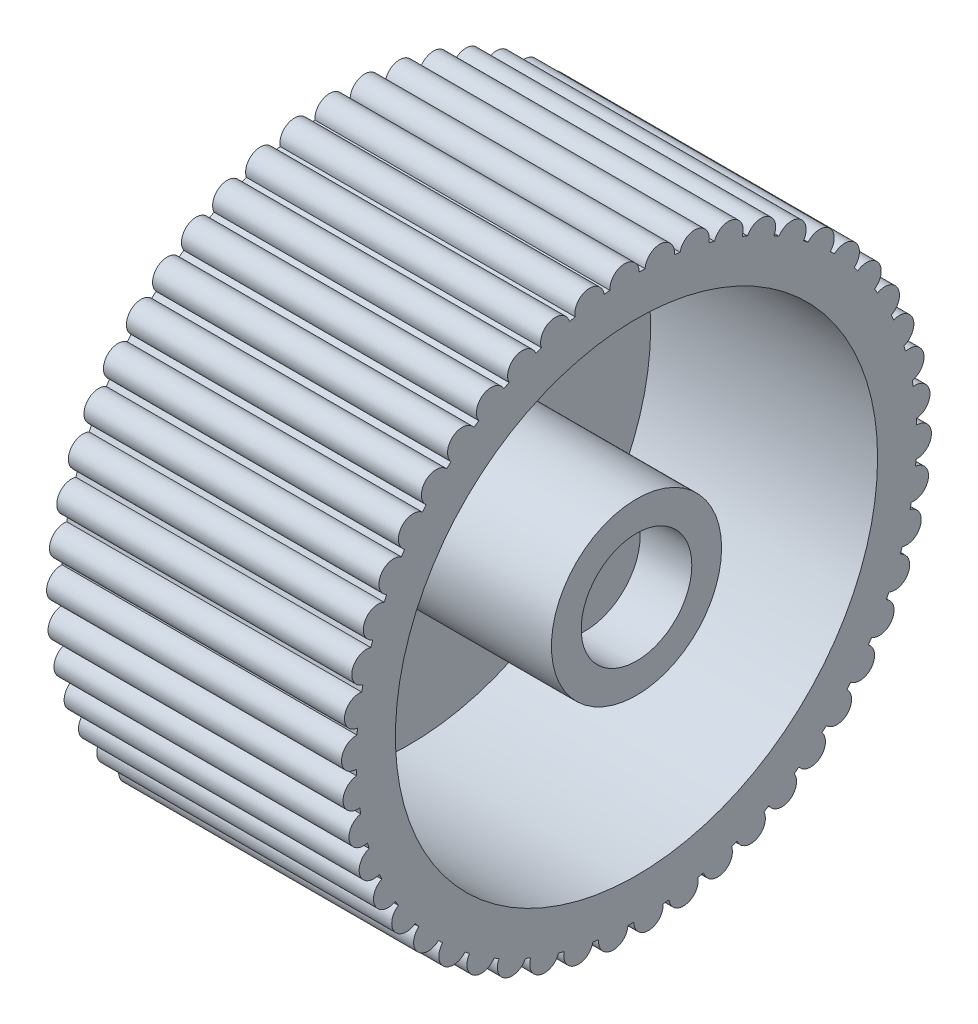
SolidWorks part; units mm, degrees
ref_plane "Front Plane" through (0, 0, 0) normal (0, 0, 1) x (1, 0, 0)
ref_plane "Top Plane" through (0, 0, 0) normal (0, 1, 0) x (1, 0, 0)
ref_plane "Right Plane" through (0, 0, 0) normal (1, 0, 0) x (0, 0, -1)
sketch "Sketch1" plane through (0, 0, 0) normal (1, 0, 0) x (0, 0, -1)
  circle A0 centre (0, 0) radius 40
  dimension "D1" = 80
extrude "Boss-Extrude1" add sketch "Sketch1" along normal blind 40
sketch "Sketch2" plane through (40, 0, 0) normal (1, 0, 0) x (0, 0, -1)
  circle A0 centre (0, 0) radius 7.5
  dimension "D1" = 15
extrude "Cut-Extrude1" cut sketch "Sketch2" against normal blind 7
sketch "Sketch3" plane through (0, 0, 0) normal (-1, 0, 0) x (0, 0, 1)
  arc A0 (-1.1654, 37.9821) -> (-5.1324, 37.6518) centre (-3.1539, 37.8776) ccw
  circle A1 centre (0, 0) radius 40
  circle A2 centre (0, 0) radius 38
  circle A3 centre (0, 0) radius 40
  arc A4 (3.6042, 37.8287) -> (-0.3729, 37.9982) centre (1.6183, 37.9742) ccw
  circle A5 centre (0, 0) radius 40
  arc A6 (8.317, 37.0787) -> (4.3925, 37.7453) centre (6.3649, 37.472) ccw
  circle A7 centre (0, 0) radius 40
  arc A8 (12.8986, 35.7439) -> (9.0886, 36.8971) centre (11.0112, 36.3788) ccw
  circle A9 centre (0, 0) radius 40
  arc A10 (17.2768, 33.8454) -> (13.6414, 35.4671) centre (15.4839, 34.7118) ccw
  circle A11 centre (0, 0) radius 40
  arc A12 (21.3825, 31.4132) -> (17.979, 33.4777) centre (19.7123, 32.4975) ccw
  circle A13 centre (0, 0) radius 40
  arc A14 (25.151, 28.4855) -> (22.0331, 30.9603) centre (23.6299, 29.7706) ccw
  circle A15 centre (0, 0) radius 40
  arc A16 (28.5229, 25.1087) -> (25.7397, 27.9547) centre (27.1748, 26.5743) ccw
  circle A17 centre (0, 0) radius 40
  arc A18 (31.4449, 21.3358) -> (29.0404, 24.5083) centre (30.2912, 22.9588) ccw
  circle A19 centre (0, 0) radius 40
  arc A20 (33.8711, 17.2265) -> (31.8831, 20.6753) centre (32.9298, 18.9813) ccw
  circle A21 centre (0, 0) radius 40
  arc A22 (35.763, 12.8455) -> (34.223, 16.5162) centre (35.0491, 14.7044) ccw
  circle A23 centre (0, 0) radius 40
  arc A24 (37.091, 8.2619) -> (36.0232, 12.0967) centre (36.6157, 10.1956) ccw
  circle A25 centre (0, 0) radius 40
  arc A26 (37.834, 3.548) -> (37.2552, 7.4864) centre (37.6048, 5.5261) ccw
  circle A27 centre (0, 0) radius 40
  arc A28 (37.9804, -1.2218) -> (37.8998, 2.7581) centre (38.0009, 0.7694) ccw
  circle A29 centre (0, 0) radius 40
  arc A30 (37.5277, -5.9724) -> (37.9466, -2.0138) centre (37.7977, -3.9995) ccw
  circle A31 centre (0, 0) radius 40
  arc A32 (36.4833, -10.6288) -> (37.395, -6.7539) centre (36.9984, -8.7053) ccw
  circle A33 centre (0, 0) radius 40
  arc A34 (34.8634, -15.1175) -> (36.2536, -11.3874) centre (35.6156, -13.2737) ccw
  circle A35 centre (0, 0) radius 40
  arc A36 (32.6938, -19.3679) -> (34.5405, -15.8414) centre (33.6711, -17.6329) ccw
  circle A37 centre (0, 0) radius 40
  arc A38 (30.0086, -23.3128) -> (32.2827, -20.0456) centre (31.1956, -21.714) ccw
  circle A39 centre (0, 0) radius 40
  arc A40 (26.8501, -26.89) -> (29.5158, -23.9336) centre (28.2281, -25.4526) ccw
  circle A41 centre (0, 0) radius 40
  arc A42 (23.2681, -30.0432) -> (26.2834, -27.4442) centre (24.8155, -28.7898) ccw
  circle A43 centre (0, 0) radius 40
  arc A44 (19.3193, -32.7226) -> (22.6364, -30.522) centre (21.0115, -31.673) ccw
  circle A45 centre (0, 0) radius 40
  arc A46 (15.0657, -34.8859) -> (18.6325, -33.1184) centre (16.8761, -34.0567) ccw
  circle A47 centre (0, 0) radius 40
  arc A48 (10.5745, -36.499) -> (14.3348, -35.1925) centre (12.4746, -35.9033) ccw
  circle A49 centre (0, 0) radius 40
  arc A50 (5.9166, -37.5366) -> (9.8109, -36.7117) centre (7.8764, -37.1837) ccw
  circle A51 centre (0, 0) radius 40
  arc A52 (1.1654, -37.9821) -> (5.1324, -37.6518) centre (3.1539, -37.8776) ccw
  circle A53 centre (0, 0) radius 40
  arc A54 (-3.6042, -37.8287) -> (0.3729, -37.9982) centre (-1.6183, -37.9742) ccw
  circle A55 centre (0, 0) radius 40
  arc A56 (-8.317, -37.0787) -> (-4.3925, -37.7453) centre (-6.3649, -37.472) ccw
  circle A57 centre (0, 0) radius 40
  arc A58 (-12.8986, -35.7439) -> (-9.0886, -36.8971) centre (-11.0112, -36.3788) ccw
  circle A59 centre (0, 0) radius 40
  arc A60 (-17.2768, -33.8454) -> (-13.6414, -35.4671) centre (-15.4839, -34.7118) ccw
  circle A61 centre (0, 0) radius 40
  arc A62 (-21.3825, -31.4132) -> (-17.979, -33.4777) centre (-19.7123, -32.4975) ccw
  circle A63 centre (0, 0) radius 40
  arc A64 (-25.151, -28.4855) -> (-22.0331, -30.9603) centre (-23.6299, -29.7706) ccw
  circle A65 centre (0, 0) radius 40
  arc A66 (-28.5229, -25.1087) -> (-25.7397, -27.9547) centre (-27.1748, -26.5743) ccw
  circle A67 centre (0, 0) radius 40
  arc A68 (-31.4449, -21.3358) -> (-29.0404, -24.5083) centre (-30.2912, -22.9588) ccw
  circle A69 centre (0, 0) radius 40
  arc A70 (-33.8711, -17.2265) -> (-31.8831, -20.6753) centre (-32.9298, -18.9813) ccw
  circle A71 centre (0, 0) radius 40
  arc A72 (-35.763, -12.8455) -> (-34.223, -16.5162) centre (-35.0491, -14.7044) ccw
  circle A73 centre (0, 0) radius 40
  arc A74 (-37.091, -8.2619) -> (-36.0232, -12.0967) centre (-36.6157, -10.1956) ccw
  circle A75 centre (0, 0) radius 40
  arc A76 (-37.834, -3.548) -> (-37.2552, -7.4864) centre (-37.6048, -5.5261) ccw
  circle A77 centre (0, 0) radius 40
  arc A78 (-37.9804, 1.2218) -> (-37.8998, -2.7581) centre (-38.0009, -0.7694) ccw
  circle A79 centre (0, 0) radius 40
  arc A80 (-37.5277, 5.9724) -> (-37.9466, 2.0138) centre (-37.7977, 3.9995) ccw
  circle A81 centre (0, 0) radius 40
  arc A82 (-36.4833, 10.6288) -> (-37.395, 6.7539) centre (-36.9984, 8.7053) ccw
  circle A83 centre (0, 0) radius 40
  arc A84 (-34.8634, 15.1175) -> (-36.2536, 11.3874) centre (-35.6156, 13.2737) ccw
  circle A85 centre (0, 0) radius 40
  arc A86 (-32.6938, 19.3679) -> (-34.5405, 15.8414) centre (-33.6711, 17.6329) ccw
  circle A87 centre (0, 0) radius 40
  arc A88 (-30.0086, 23.3128) -> (-32.2827, 20.0456) centre (-31.1956, 21.714) ccw
  circle A89 centre (0, 0) radius 40
  arc A90 (-26.8501, 26.89) -> (-29.5158, 23.9336) centre (-28.2281, 25.4526) ccw
  circle A91 centre (0, 0) radius 40
  arc A92 (-23.2681, 30.0432) -> (-26.2834, 27.4442) centre (-24.8155, 28.7898) ccw
  circle A93 centre (0, 0) radius 40
  arc A94 (-19.3193, 32.7226) -> (-22.6364, 30.522) centre (-21.0115, 31.673) ccw
  circle A95 centre (0, 0) radius 40
  arc A96 (-15.0657, 34.8859) -> (-18.6325, 33.1184) centre (-16.8761, 34.0567) ccw
  circle A97 centre (0, 0) radius 40
  arc A98 (-10.5745, 36.499) -> (-14.3348, 35.1925) centre (-12.4746, 35.9033) ccw
  circle A99 centre (0, 0) radius 40
  arc A100 (-5.9166, 37.5366) -> (-9.8109, 36.7117) centre (-7.8764, 37.1837) ccw
  point P207 (0, 0)
  circle M4 centre (0, 0) radius 40
  dimension "D1" = 2
  dimension "D2" = 50
extrude "Cut-Extrude2" cut sketch "Sketch3" against normal through all contours A90 A89 A88 A2 | A92 A91 A90 A2 | A94 A93 A92 A2 | A96 A95 A94 A2 | A98 A97 A96 A2 | A100 A99 A98 A2 | A100 A2 A0 M4 | A4 A3 A0 A2 | A6 A5 A4 A2 | A8 A7 A6 A2 | A10 A9 A8 A2 | A12 A11 A10 A2 | A14 A13 A12 A2 | A16 A15 A14 A2 | A18 A17 A16 A2 | A20 A19 A18 A2 | A22 A21 A20 A2 | A24 A23 A22 A2 | A26 A25 A24 A2 | A28 A27 A26 A2 | A30 A29 A28 A2 | A32 A31 A30 A2 | A34 A33 A32 A2 | A36 A35 A34 A2 | A38 A37 A36 A2 | A40 A39 A38 A2 | A42 A41 A40 A2 | A44 A43 A42 A2 | A46 A45 A44 A2 | A48 A47 A46 A2 | A50 A49 A48 A2 | A88 A87 A86 A2 | A86 A85 A84 A2 | A84 A83 A82 A2 | A82 A81 A80 A2 | A80 A79 A78 A2 | A78 A77 A76 A2 | A76 A75 A74 A2 | A74 A73 A72 A2 | A72 A71 A70 A2 | A70 A69 A68 A2 | A68 A67 A66 A2 | A66 A65 A64 A2 | A64 A63 A62 A2 | A62 A61 A60 A2 | A60 A59 A58 A2 | A58 A57 A56 A2 | A56 A55 A54 A2 | A54 A53 A52 A2 | A52 A51 A50 A2
scale "Scale1" bodies to scale 103 scale about centroid uniform scaling yes scale factor 1.3
sketch "Sketch4" plane through (46.0317, 0, 0) normal (1, 0, 0) x (0, 0, -1)
  circle A0 centre (0, 0) radius 15
  circle A1 centre (0, 0) radius 42.5
  dimension "D1" = 30
  dimension "D2" = 85
extrude "Cut-Extrude4" cut sketch "Sketch4" against normal blind 40
